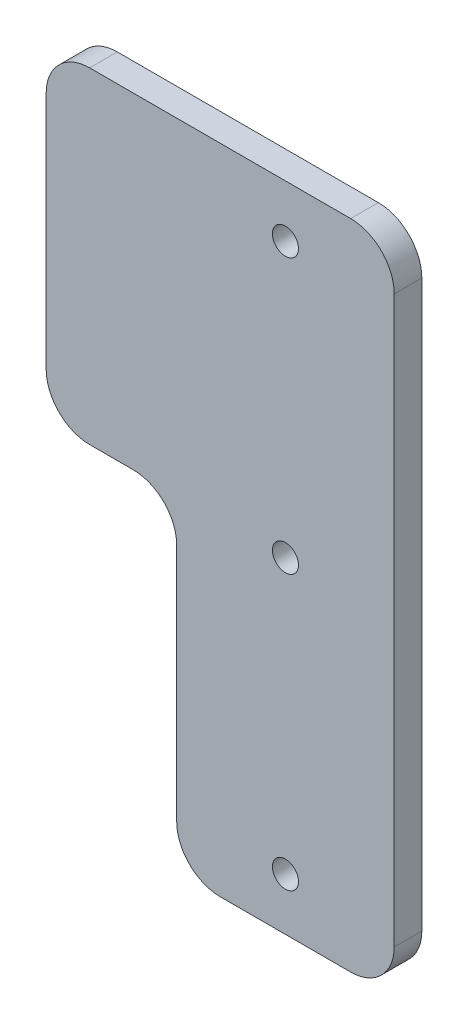
SolidWorks part; units mm, degrees
ref_plane "Front Plane" through (0, 0, 0) normal (0, 0, 1) x (1, 0, 0)
ref_plane "Top Plane" through (0, 0, 0) normal (0, 1, 0) x (1, 0, 0)
ref_plane "Right Plane" through (0, 0, 0) normal (1, 0, 0) x (0, 0, -1)
sketch "Sketch1" plane through (0, 0, 0) normal (0, 0, 1) x (1, 0, 0)
  line L0 (12.5, 69) -> (12.5, 6) construction
  line L1 (0, 0) -> (25, 0)
  line L2 (0, 0) -> (0, 75)
  line L3 (0, 75) -> (25, 75)
  line L4 (25, 0) -> (25, 75)
  line L6 (0, 75) -> (-15, 75)
  line L7 (0, 75) -> (0, 37.5)
  line L8 (0, 37.5) -> (-15, 37.5)
  line L9 (-15, 75) -> (-15, 37.5)
  circle A0 centre (12.5, 69) radius 1.5
  circle A1 centre (12.5, 6) radius 1.5
  circle A2 centre (12.5, 37.5) radius 1.5
  dimension "D3" = 3
  dimension "D4" = 3
  dimension "D7" = 3
  dimension "D1" = 75
  dimension "D2" = 25
  dimension "D5" = 6
  dimension "D6" = 6
  dimension "D8" = 0
  dimension "D9" = 12.5
  dimension "D10" = 15
extrude "Boss-Extrude1" add sketch "Sketch1" along normal blind 3.175
fillet "Fillet1" radius 5 6 edges at (25, 0, 1.5875) (0, 0, 1.5875) (25, 75, 1.5875) (-15, 75, 1.5875) (-15, 37.5, 1.5875) (0, 37.5, 1.5875)
